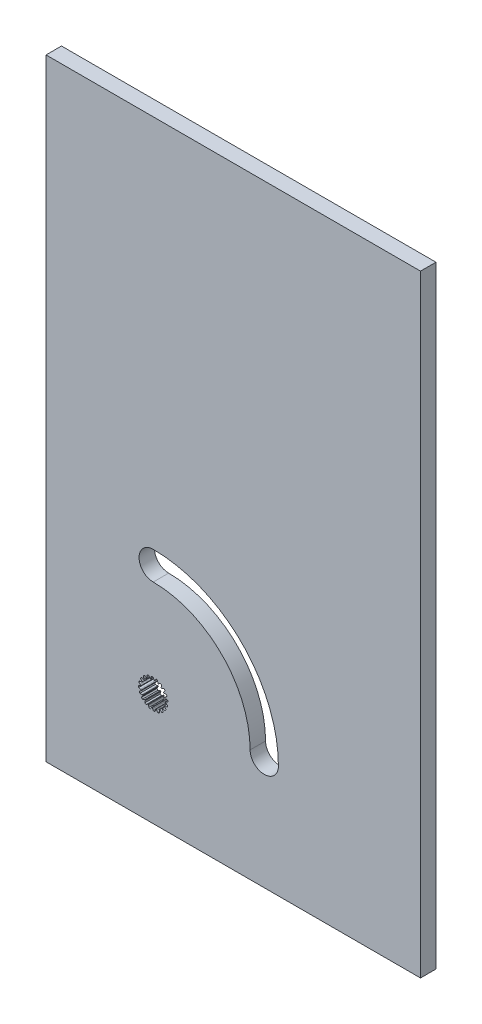
SolidWorks part; units mm, degrees
ref_plane "Ön Düzlem" through (0, 0, 0) normal (0, 0, 1) x (1, 0, 0)
ref_plane "Üst Düzlem" through (0, 0, 0) normal (0, 1, 0) x (1, 0, 0)
ref_plane "Sağ Düzlem" through (0, 0, 0) normal (1, 0, 0) x (0, 0, -1)
sketch "Çizim1" plane through (0, 0, 0) normal (0, 0, 1) x (1, 0, 0)
  line L1 (-41.8204, 26.3508) -> (30.9359, 26.3508)
  line L2 (-41.8204, 26.3508) -> (-41.8204, -92.5962)
  line L3 (-41.8204, -92.5962) -> (30.9359, -92.5962)
  line L4 (30.9359, 26.3508) -> (30.9359, -92.5962)
  point P11 (-21.6285, -56.4542)
extrude "Yükseklik-Ekstrüzyon1" add sketch "Çizim1" along normal blind 3
sketch "Çizim4" plane through (0, 0, 0) normal (0, 0, -1) x (-1, 0, 0)
  line L0 (20.655, -68.2535) -> (20.4495, -67.9708)
  line L1 (20.1545, -68.0456) -> (20.1085, -68.392)
  line L2 (20.1085, -68.392) -> (20.1196, -68.5886)
  line L3 (20.0301, -68.627) -> (19.8953, -68.4835)
  line L4 (19.8953, -68.4835) -> (19.6125, -68.2782)
  line L5 (19.355, -68.4404) -> (19.4183, -68.7841)
  line L6 (19.4183, -68.7841) -> (19.4896, -68.9677)
  line L7 (19.4164, -69.0318) -> (19.2438, -68.937)
  line L8 (19.2438, -68.937) -> (18.9114, -68.8291)
  line L9 (18.7167, -69.063) -> (18.8831, -69.3703)
  line L10 (18.8831, -69.3703) -> (19.0076, -69.5229)
  line L11 (18.9578, -69.6065) -> (18.7644, -69.5697)
  line L12 (18.7644, -69.5697) -> (18.4149, -69.5698)
  line L13 (18.302, -69.8524) -> (18.5552, -70.0933)
  line L14 (18.5552, -70.0933) -> (18.7207, -70.1998)
  line L15 (18.6992, -70.2948) -> (18.5039, -70.3195)
  line L16 (18.5039, -70.3195) -> (18.1716, -70.4276)
  line L17 (18.1515, -70.7313) -> (18.4668, -70.8821)
  line L18 (18.4668, -70.8821) -> (18.6571, -70.9323)
  line L19 (18.666, -71.0293) -> (18.4879, -71.1132)
  line L20 (18.4879, -71.1132) -> (18.2052, -71.3187)
  line L21 (18.28, -71.6137) -> (18.6264, -71.6597)
  line L22 (18.6264, -71.6597) -> (18.823, -71.6486)
  line L23 (18.8614, -71.7381) -> (18.7179, -71.8729)
  line L24 (18.7179, -71.8729) -> (18.5126, -72.1557)
  line L25 (18.6749, -72.4132) -> (19.0185, -72.3499)
  line L26 (19.0185, -72.3499) -> (19.2021, -72.2786)
  line L27 (19.2662, -72.3518) -> (19.1715, -72.5244)
  line L28 (19.1715, -72.5244) -> (19.0636, -72.8568)
  line L29 (19.2975, -73.0515) -> (19.6048, -72.8851)
  line L30 (19.6048, -72.8851) -> (19.7573, -72.7606)
  line L31 (19.8409, -72.8104) -> (19.8041, -73.0038)
  line L32 (19.8041, -73.0038) -> (19.8042, -73.3533)
  line L33 (20.0868, -73.4662) -> (20.3277, -73.213)
  line L34 (20.3277, -73.213) -> (20.4343, -73.0474)
  line L35 (20.5292, -73.069) -> (20.554, -73.2643)
  line L36 (20.554, -73.2643) -> (20.6621, -73.5966)
  line L37 (20.9657, -73.6167) -> (21.1165, -73.3014)
  line L38 (21.1165, -73.3014) -> (21.1668, -73.111)
  line L39 (21.2637, -73.1022) -> (21.3476, -73.2803)
  line L40 (21.3476, -73.2803) -> (21.5531, -73.563)
  line L41 (21.8481, -73.4882) -> (21.8941, -73.1418)
  line L42 (21.8941, -73.1418) -> (21.883, -72.9452)
  line L43 (21.9725, -72.9068) -> (22.1074, -73.0503)
  line L44 (22.1074, -73.0503) -> (22.3901, -73.2556)
  line L45 (22.6476, -73.0933) -> (22.5843, -72.7496)
  line L46 (22.5843, -72.7496) -> (22.513, -72.5661)
  line L47 (22.5862, -72.5019) -> (22.7588, -72.5967)
  line L48 (22.7588, -72.5967) -> (23.0912, -72.7046)
  line L49 (23.2859, -72.4707) -> (23.1195, -72.1634)
  line L50 (23.1195, -72.1634) -> (22.995, -72.0109)
  line L51 (23.0448, -71.9273) -> (23.2383, -71.9641)
  line L52 (23.2383, -71.9641) -> (23.5877, -71.964)
  line L53 (23.7006, -71.6813) -> (23.4474, -71.4405)
  line L54 (23.4474, -71.4405) -> (23.2819, -71.3339)
  line L55 (23.3034, -71.239) -> (23.4987, -71.2142)
  line L56 (23.4987, -71.2142) -> (23.831, -71.1061)
  line L57 (23.8511, -70.8025) -> (23.5359, -70.6516)
  line L58 (23.5359, -70.6516) -> (23.3455, -70.6014)
  line L59 (23.3366, -70.5045) -> (23.5147, -70.4206)
  line L60 (23.5147, -70.4206) -> (23.7974, -70.2151)
  line L61 (23.7226, -69.9201) -> (23.3762, -69.8741)
  line L62 (23.3762, -69.8741) -> (23.1796, -69.8851)
  line L63 (23.1412, -69.7957) -> (23.2847, -69.6608)
  line L64 (23.2847, -69.6608) -> (23.49, -69.3781)
  line L65 (23.3277, -69.1206) -> (22.9841, -69.1839)
  line L66 (22.9841, -69.1839) -> (22.8005, -69.2552)
  line L67 (22.7364, -69.1819) -> (22.8312, -69.0094)
  line L68 (22.8312, -69.0094) -> (22.939, -68.677)
  line L69 (22.7052, -68.4823) -> (22.3979, -68.6487)
  line L70 (22.3979, -68.6487) -> (22.2453, -68.7732)
  line L71 (22.1617, -68.7233) -> (22.1985, -68.5299)
  line L72 (22.1985, -68.5299) -> (22.1984, -68.1805)
  line L73 (21.9158, -68.0676) -> (21.6749, -68.3208)
  line L74 (21.6749, -68.3208) -> (21.5683, -68.4863)
  line L75 (21.4734, -68.4648) -> (21.4486, -68.2695)
  line L76 (21.4486, -68.2695) -> (21.3406, -67.9371)
  line L77 (21.0369, -67.9171) -> (20.8861, -68.2323)
  line L78 (20.8861, -68.2323) -> (20.8359, -68.4227)
  line L79 (20.7389, -68.4316) -> (20.655, -68.2535)
  line L80 (20.5686, -68.3046) -> (20.4067, -68.0819)
  line L81 (20.2451, -68.1229) -> (20.2089, -68.3958)
  line L82 (20.2089, -68.3958) -> (20.2235, -68.6556)
  line L83 (20.0071, -68.7485) -> (19.8289, -68.5589)
  line L84 (19.8289, -68.5589) -> (19.6061, -68.3971)
  line L85 (19.4651, -68.486) -> (19.5149, -68.7567)
  line L86 (19.5149, -68.7567) -> (19.6091, -68.9993)
  line L87 (19.432, -69.1545) -> (19.2039, -69.0292)
  line L88 (19.2039, -69.0292) -> (18.9421, -68.9442)
  line L89 (18.8354, -69.0723) -> (18.9665, -69.3144)
  line L90 (18.9665, -69.3144) -> (19.1311, -69.516)
  line L91 (19.0106, -69.7183) -> (18.7549, -69.6697)
  line L92 (18.7549, -69.6697) -> (18.4796, -69.6698)
  line L93 (18.4178, -69.8245) -> (18.6173, -70.0143)
  line L94 (18.6173, -70.0143) -> (18.8361, -70.1552)
  line L95 (18.784, -70.3848) -> (18.5258, -70.4176)
  line L96 (18.5258, -70.4176) -> (18.264, -70.5027)
  line L97 (18.253, -70.669) -> (18.5014, -70.7878)
  line L98 (18.5014, -70.7878) -> (18.753, -70.8542)
  line L99 (18.7744, -71.0887) -> (18.539, -71.1996)
  line L100 (18.539, -71.1996) -> (18.3164, -71.3615)
  line L101 (18.3573, -71.5231) -> (18.6302, -71.5593)
  line L102 (18.6302, -71.5593) -> (18.89, -71.5447)
  line L103 (18.9829, -71.7611) -> (18.7933, -71.9393)
  line L104 (18.7933, -71.9393) -> (18.6315, -72.1621)
  line L105 (18.7204, -72.3031) -> (18.9912, -72.2532)
  line L106 (18.9912, -72.2532) -> (19.2337, -72.159)
  line L107 (19.3889, -72.3362) -> (19.2637, -72.5643)
  line L108 (19.2637, -72.5643) -> (19.1787, -72.8261)
  line L109 (19.3067, -72.9327) -> (19.5488, -72.8017)
  line L110 (19.5488, -72.8017) -> (19.7504, -72.6371)
  line L111 (19.9528, -72.7576) -> (19.9041, -73.0133)
  line L112 (19.9041, -73.0133) -> (19.9042, -73.2886)
  line L113 (20.059, -73.3504) -> (20.2487, -73.1509)
  line L114 (20.2487, -73.1509) -> (20.3896, -72.9321)
  line L115 (20.6193, -72.9842) -> (20.652, -73.2424)
  line L116 (20.652, -73.2424) -> (20.7371, -73.5042)
  line L117 (20.9034, -73.5151) -> (21.0223, -73.2668)
  line L118 (21.0223, -73.2668) -> (21.0886, -73.0152)
  line L119 (21.3232, -72.9937) -> (21.434, -73.2291)
  line L120 (21.434, -73.2291) -> (21.5959, -73.4518)
  line L121 (21.7575, -73.4109) -> (21.7937, -73.138)
  line L122 (21.7937, -73.138) -> (21.7791, -72.8782)
  line L123 (21.9955, -72.7853) -> (22.1738, -72.9749)
  line L124 (22.1738, -72.9749) -> (22.3965, -73.1367)
  line L125 (22.5375, -73.0478) -> (22.4877, -72.777)
  line L126 (22.4877, -72.777) -> (22.3935, -72.5345)
  line L127 (22.5706, -72.3793) -> (22.7987, -72.5045)
  line L128 (22.7987, -72.5045) -> (23.0605, -72.5895)
  line L129 (23.1672, -72.4614) -> (23.0361, -72.2193)
  line L130 (23.0361, -72.2193) -> (22.8715, -72.0178)
  line L131 (22.9921, -71.8154) -> (23.2477, -71.8641)
  line L132 (23.2477, -71.8641) -> (23.523, -71.864)
  line L133 (23.5848, -71.7092) -> (23.3853, -71.5195)
  line L134 (23.3853, -71.5195) -> (23.1666, -71.3786)
  line L135 (23.2186, -71.1489) -> (23.4768, -71.1162)
  line L136 (23.4768, -71.1162) -> (23.7386, -71.0311)
  line L137 (23.7496, -70.8647) -> (23.5012, -70.7459)
  line L138 (23.5012, -70.7459) -> (23.2496, -70.6796)
  line L139 (23.2282, -70.445) -> (23.4636, -70.3341)
  line L140 (23.4636, -70.3341) -> (23.6863, -70.1723)
  line L141 (23.6453, -70.0107) -> (23.3724, -69.9744)
  line L142 (23.3724, -69.9744) -> (23.1126, -69.9891)
  line L143 (23.0197, -69.7726) -> (23.2093, -69.5944)
  line L144 (23.2093, -69.5944) -> (23.3711, -69.3717)
  line L145 (23.2822, -69.2307) -> (23.0115, -69.2805)
  line L146 (23.0115, -69.2805) -> (22.7689, -69.3747)
  line L147 (22.6137, -69.1976) -> (22.739, -68.9695)
  line L148 (22.739, -68.9695) -> (22.824, -68.7076)
  line L149 (22.6959, -68.601) -> (22.4538, -68.7321)
  line L150 (22.4538, -68.7321) -> (22.2522, -68.8966)
  line L151 (22.0498, -68.7761) -> (22.0985, -68.5205)
  line L152 (22.0985, -68.5205) -> (22.0984, -68.2452)
  line L153 (21.9436, -68.1834) -> (21.7539, -68.3828)
  line L154 (21.7539, -68.3828) -> (21.613, -68.6016)
  line L155 (21.3833, -68.5496) -> (21.3506, -68.2914)
  line L156 (21.3506, -68.2914) -> (21.2655, -68.0296)
  line L157 (21.0992, -68.0186) -> (20.9804, -68.267)
  line L158 (20.9804, -68.267) -> (20.914, -68.5186)
  line L159 (20.6795, -68.54) -> (20.5686, -68.3046)
  line L160 (20.5686, -68.3046) -> (20.4067, -68.0819)
  line L161 (20.2451, -68.1229) -> (20.2089, -68.3958)
  line L162 (20.2089, -68.3958) -> (20.2235, -68.6556)
  line L163 (20.0071, -68.7485) -> (19.8289, -68.5589)
  line L164 (19.8289, -68.5589) -> (19.6061, -68.3971)
  line L165 (19.4651, -68.486) -> (19.5149, -68.7567)
  line L166 (19.5149, -68.7567) -> (19.6091, -68.9993)
  line L167 (19.432, -69.1545) -> (19.2039, -69.0292)
  line L168 (19.2039, -69.0292) -> (18.9421, -68.9442)
  line L169 (18.8354, -69.0723) -> (18.9665, -69.3144)
  line L170 (18.9665, -69.3144) -> (19.1311, -69.516)
  line L171 (19.0106, -69.7183) -> (18.7549, -69.6697)
  line L172 (18.7549, -69.6697) -> (18.4796, -69.6698)
  line L173 (18.4178, -69.8245) -> (18.6173, -70.0143)
  line L174 (18.6173, -70.0143) -> (18.8361, -70.1552)
  line L175 (18.784, -70.3848) -> (18.5258, -70.4176)
  line L176 (18.5258, -70.4176) -> (18.264, -70.5027)
  line L177 (18.253, -70.669) -> (18.5014, -70.7878)
  line L178 (18.5014, -70.7878) -> (18.753, -70.8542)
  line L179 (18.7744, -71.0887) -> (18.539, -71.1996)
  line L180 (18.539, -71.1996) -> (18.3164, -71.3615)
  line L181 (18.3573, -71.5231) -> (18.6302, -71.5593)
  line L182 (18.6302, -71.5593) -> (18.89, -71.5447)
  line L183 (18.9829, -71.7611) -> (18.7933, -71.9393)
  line L184 (18.7933, -71.9393) -> (18.6315, -72.1621)
  line L185 (18.7204, -72.3031) -> (18.9912, -72.2532)
  line L186 (18.9912, -72.2532) -> (19.2337, -72.159)
  line L187 (19.3889, -72.3362) -> (19.2637, -72.5643)
  line L188 (19.2637, -72.5643) -> (19.1787, -72.8261)
  line L189 (19.3067, -72.9327) -> (19.5488, -72.8017)
  line L190 (19.5488, -72.8017) -> (19.7504, -72.6371)
  line L191 (19.9528, -72.7576) -> (19.9041, -73.0133)
  line L192 (19.9041, -73.0133) -> (19.9042, -73.2886)
  line L193 (20.059, -73.3504) -> (20.2487, -73.1509)
  line L194 (20.2487, -73.1509) -> (20.3896, -72.9321)
  line L195 (20.6193, -72.9842) -> (20.652, -73.2424)
  line L196 (20.652, -73.2424) -> (20.7371, -73.5042)
  line L197 (20.9034, -73.5151) -> (21.0223, -73.2668)
  line L198 (21.0223, -73.2668) -> (21.0886, -73.0152)
  line L199 (21.3232, -72.9937) -> (21.434, -73.2291)
  line L200 (21.434, -73.2291) -> (21.5959, -73.4518)
  line L201 (21.7575, -73.4109) -> (21.7937, -73.138)
  line L202 (21.7937, -73.138) -> (21.7791, -72.8782)
  line L203 (21.9955, -72.7853) -> (22.1738, -72.9749)
  line L204 (22.1738, -72.9749) -> (22.3965, -73.1367)
  line L205 (22.5375, -73.0478) -> (22.4877, -72.777)
  line L206 (22.4877, -72.777) -> (22.3935, -72.5345)
  line L207 (22.5706, -72.3793) -> (22.7987, -72.5045)
  line L208 (22.7987, -72.5045) -> (23.0605, -72.5895)
  line L209 (23.1672, -72.4614) -> (23.0361, -72.2193)
  line L210 (23.0361, -72.2193) -> (22.8715, -72.0178)
  line L211 (22.9921, -71.8154) -> (23.2477, -71.8641)
  line L212 (23.2477, -71.8641) -> (23.523, -71.864)
  line L213 (23.5848, -71.7092) -> (23.3853, -71.5195)
  line L214 (23.3853, -71.5195) -> (23.1666, -71.3786)
  line L215 (23.2186, -71.1489) -> (23.4768, -71.1162)
  line L216 (23.4768, -71.1162) -> (23.7386, -71.0311)
  line L217 (23.7496, -70.8647) -> (23.5012, -70.7459)
  line L218 (23.5012, -70.7459) -> (23.2496, -70.6796)
  line L219 (23.2282, -70.445) -> (23.4636, -70.3341)
  line L220 (23.4636, -70.3341) -> (23.6863, -70.1723)
  line L221 (23.6453, -70.0107) -> (23.3724, -69.9744)
  line L222 (23.3724, -69.9744) -> (23.1126, -69.9891)
  line L223 (23.0197, -69.7726) -> (23.2093, -69.5944)
  line L224 (23.2093, -69.5944) -> (23.3711, -69.3717)
  line L225 (23.2822, -69.2307) -> (23.0115, -69.2805)
  line L226 (23.0115, -69.2805) -> (22.7689, -69.3747)
  line L227 (22.6137, -69.1976) -> (22.739, -68.9695)
  line L228 (22.739, -68.9695) -> (22.824, -68.7076)
  line L229 (22.6959, -68.601) -> (22.4538, -68.7321)
  line L230 (22.4538, -68.7321) -> (22.2522, -68.8966)
  line L231 (22.0498, -68.7761) -> (22.0985, -68.5205)
  line L232 (22.0985, -68.5205) -> (22.0984, -68.2452)
  line L233 (21.9436, -68.1834) -> (21.7539, -68.3828)
  line L234 (21.7539, -68.3828) -> (21.613, -68.6016)
  line L235 (21.3833, -68.5496) -> (21.3506, -68.2914)
  line L236 (21.3506, -68.2914) -> (21.2655, -68.0296)
  line L237 (21.0992, -68.0186) -> (20.9804, -68.267)
  line L238 (20.9804, -68.267) -> (20.914, -68.5186)
  line L239 (20.6795, -68.54) -> (20.5686, -68.3046)
  arc A0 (20.4495, -67.9708) -> (20.1545, -68.0456) centre (21.0013, -70.7669) ccw
  arc A1 (20.1196, -68.5886) -> (20.0301, -68.627) centre (21.0013, -70.7669) ccw
  arc A2 (19.6125, -68.2782) -> (19.355, -68.4404) centre (21.0013, -70.7669) ccw
  arc A3 (19.4896, -68.9677) -> (19.4164, -69.0318) centre (21.0013, -70.7669) ccw
  arc A4 (18.9114, -68.8291) -> (18.7167, -69.063) centre (21.0013, -70.7669) ccw
  arc A5 (19.0076, -69.5229) -> (18.9578, -69.6065) centre (21.0013, -70.7669) ccw
  arc A6 (18.4149, -69.5698) -> (18.302, -69.8524) centre (21.0013, -70.7669) ccw
  arc A7 (18.7207, -70.1998) -> (18.6992, -70.2948) centre (21.0013, -70.7669) ccw
  arc A8 (18.1716, -70.4276) -> (18.1515, -70.7313) centre (21.0013, -70.7669) ccw
  arc A9 (18.6571, -70.9323) -> (18.666, -71.0293) centre (21.0013, -70.7669) ccw
  arc A10 (18.2052, -71.3187) -> (18.28, -71.6137) centre (21.0013, -70.7669) ccw
  arc A11 (18.823, -71.6486) -> (18.8614, -71.7381) centre (21.0013, -70.7669) ccw
  arc A12 (18.5126, -72.1557) -> (18.6749, -72.4132) centre (21.0013, -70.7669) ccw
  arc A13 (19.2021, -72.2786) -> (19.2662, -72.3518) centre (21.0013, -70.7669) ccw
  arc A14 (19.0636, -72.8568) -> (19.2975, -73.0515) centre (21.0013, -70.7669) ccw
  arc A15 (19.7573, -72.7606) -> (19.8409, -72.8104) centre (21.0013, -70.7669) ccw
  arc A16 (19.8042, -73.3533) -> (20.0868, -73.4662) centre (21.0013, -70.7669) ccw
  arc A17 (20.4343, -73.0474) -> (20.5292, -73.069) centre (21.0013, -70.7669) ccw
  arc A18 (20.6621, -73.5966) -> (20.9657, -73.6167) centre (21.0013, -70.7669) ccw
  arc A19 (21.1668, -73.111) -> (21.2637, -73.1022) centre (21.0013, -70.7669) ccw
  arc A20 (21.5531, -73.563) -> (21.8481, -73.4882) centre (21.0013, -70.7669) ccw
  arc A21 (21.883, -72.9452) -> (21.9725, -72.9068) centre (21.0013, -70.7669) ccw
  arc A22 (22.3901, -73.2556) -> (22.6476, -73.0933) centre (21.0013, -70.7669) ccw
  arc A23 (22.513, -72.5661) -> (22.5862, -72.5019) centre (21.0013, -70.7669) ccw
  arc A24 (23.0912, -72.7046) -> (23.2859, -72.4707) centre (21.0013, -70.7669) ccw
  arc A25 (22.995, -72.0109) -> (23.0448, -71.9273) centre (21.0013, -70.7669) ccw
  arc A26 (23.5877, -71.964) -> (23.7006, -71.6813) centre (21.0013, -70.7669) ccw
  arc A27 (23.2819, -71.3339) -> (23.3034, -71.239) centre (21.0013, -70.7669) ccw
  arc A28 (23.831, -71.1061) -> (23.8511, -70.8025) centre (21.0013, -70.7669) ccw
  arc A29 (23.3455, -70.6014) -> (23.3366, -70.5045) centre (21.0013, -70.7669) ccw
  arc A30 (23.7974, -70.2151) -> (23.7226, -69.9201) centre (21.0013, -70.7669) ccw
  arc A31 (23.1796, -69.8851) -> (23.1412, -69.7957) centre (21.0013, -70.7669) ccw
  arc A32 (23.49, -69.3781) -> (23.3277, -69.1206) centre (21.0013, -70.7669) ccw
  arc A33 (22.8005, -69.2552) -> (22.7364, -69.1819) centre (21.0013, -70.7669) ccw
  arc A34 (22.939, -68.677) -> (22.7052, -68.4823) centre (21.0013, -70.7669) ccw
  arc A35 (22.2453, -68.7732) -> (22.1617, -68.7233) centre (21.0013, -70.7669) ccw
  arc A36 (22.1984, -68.1805) -> (21.9158, -68.0676) centre (21.0013, -70.7669) ccw
  arc A37 (21.5683, -68.4863) -> (21.4734, -68.4648) centre (21.0013, -70.7669) ccw
  arc A38 (21.3406, -67.9371) -> (21.0369, -67.9171) centre (21.0013, -70.7669) ccw
  arc A39 (20.8359, -68.4227) -> (20.7389, -68.4316) centre (21.0013, -70.7669) ccw
  arc A40 (20.4067, -68.0819) -> (20.2451, -68.1229) centre (21.0013, -70.7669) ccw
  arc A41 (20.2235, -68.6556) -> (20.0071, -68.7485) centre (21.0013, -70.7669) ccw
  arc A42 (19.6061, -68.3971) -> (19.4651, -68.486) centre (21.0013, -70.7669) ccw
  arc A43 (19.6091, -68.9993) -> (19.432, -69.1545) centre (21.0013, -70.7669) ccw
  arc A44 (18.9421, -68.9442) -> (18.8354, -69.0723) centre (21.0013, -70.7669) ccw
  arc A45 (19.1311, -69.516) -> (19.0106, -69.7183) centre (21.0013, -70.7669) ccw
  arc A46 (18.4796, -69.6698) -> (18.4178, -69.8245) centre (21.0013, -70.7669) ccw
  arc A47 (18.8361, -70.1552) -> (18.784, -70.3848) centre (21.0013, -70.7669) ccw
  arc A48 (18.264, -70.5027) -> (18.253, -70.669) centre (21.0013, -70.7669) ccw
  arc A49 (18.753, -70.8542) -> (18.7744, -71.0887) centre (21.0013, -70.7669) ccw
  arc A50 (18.3164, -71.3615) -> (18.3573, -71.5231) centre (21.0013, -70.7669) ccw
  arc A51 (18.89, -71.5447) -> (18.9829, -71.7611) centre (21.0013, -70.7669) ccw
  arc A52 (18.6315, -72.1621) -> (18.7204, -72.3031) centre (21.0013, -70.7669) ccw
  arc A53 (19.2337, -72.159) -> (19.3889, -72.3362) centre (21.0013, -70.7669) ccw
  arc A54 (19.1787, -72.8261) -> (19.3067, -72.9327) centre (21.0013, -70.7669) ccw
  arc A55 (19.7504, -72.6371) -> (19.9528, -72.7576) centre (21.0013, -70.7669) ccw
  arc A56 (19.9042, -73.2886) -> (20.059, -73.3504) centre (21.0013, -70.7669) ccw
  arc A57 (20.3896, -72.9321) -> (20.6193, -72.9842) centre (21.0013, -70.7669) ccw
  arc A58 (20.7371, -73.5042) -> (20.9034, -73.5151) centre (21.0013, -70.7669) ccw
  arc A59 (21.0886, -73.0152) -> (21.3232, -72.9937) centre (21.0013, -70.7669) ccw
  arc A60 (21.5959, -73.4518) -> (21.7575, -73.4109) centre (21.0013, -70.7669) ccw
  arc A61 (21.7791, -72.8782) -> (21.9955, -72.7853) centre (21.0013, -70.7669) ccw
  arc A62 (22.3965, -73.1367) -> (22.5375, -73.0478) centre (21.0013, -70.7669) ccw
  arc A63 (22.3935, -72.5345) -> (22.5706, -72.3793) centre (21.0013, -70.7669) ccw
  arc A64 (23.0605, -72.5895) -> (23.1672, -72.4614) centre (21.0013, -70.7669) ccw
  arc A65 (22.8715, -72.0178) -> (22.9921, -71.8154) centre (21.0013, -70.7669) ccw
  arc A66 (23.523, -71.864) -> (23.5848, -71.7092) centre (21.0013, -70.7669) ccw
  arc A67 (23.1666, -71.3786) -> (23.2186, -71.1489) centre (21.0013, -70.7669) ccw
  arc A68 (23.7386, -71.0311) -> (23.7496, -70.8647) centre (21.0013, -70.7669) ccw
  arc A69 (23.2496, -70.6796) -> (23.2282, -70.445) centre (21.0013, -70.7669) ccw
  arc A70 (23.6863, -70.1723) -> (23.6453, -70.0107) centre (21.0013, -70.7669) ccw
  arc A71 (23.1126, -69.9891) -> (23.0197, -69.7726) centre (21.0013, -70.7669) ccw
  arc A72 (23.3711, -69.3717) -> (23.2822, -69.2307) centre (21.0013, -70.7669) ccw
  arc A73 (22.7689, -69.3747) -> (22.6137, -69.1976) centre (21.0013, -70.7669) ccw
  arc A74 (22.824, -68.7076) -> (22.6959, -68.601) centre (21.0013, -70.7669) ccw
  arc A75 (22.2522, -68.8966) -> (22.0498, -68.7761) centre (21.0013, -70.7669) ccw
  arc A76 (22.0984, -68.2452) -> (21.9436, -68.1834) centre (21.0013, -70.7669) ccw
  arc A77 (21.613, -68.6016) -> (21.3833, -68.5496) centre (21.0013, -70.7669) ccw
  arc A78 (21.2655, -68.0296) -> (21.0992, -68.0186) centre (21.0013, -70.7669) ccw
  arc A79 (20.914, -68.5186) -> (20.6795, -68.54) centre (21.0013, -70.7669) ccw
  arc A80 (20.4067, -68.0819) -> (20.2451, -68.1229) centre (21.0013, -70.7669) ccw
  arc A81 (20.2235, -68.6556) -> (20.0071, -68.7485) centre (21.0013, -70.7669) ccw
  arc A82 (19.6061, -68.3971) -> (19.4651, -68.486) centre (21.0013, -70.7669) ccw
  arc A83 (19.6091, -68.9993) -> (19.432, -69.1545) centre (21.0013, -70.7669) ccw
  arc A84 (18.9421, -68.9442) -> (18.8354, -69.0723) centre (21.0013, -70.7669) ccw
  arc A85 (19.1311, -69.516) -> (19.0106, -69.7183) centre (21.0013, -70.7669) ccw
  arc A86 (18.4796, -69.6698) -> (18.4178, -69.8245) centre (21.0013, -70.7669) ccw
  arc A87 (18.8361, -70.1552) -> (18.784, -70.3848) centre (21.0013, -70.7669) ccw
  arc A88 (18.264, -70.5027) -> (18.253, -70.669) centre (21.0013, -70.7669) ccw
  arc A89 (18.753, -70.8542) -> (18.7744, -71.0887) centre (21.0013, -70.7669) ccw
  arc A90 (18.3164, -71.3615) -> (18.3573, -71.5231) centre (21.0013, -70.7669) ccw
  arc A91 (18.89, -71.5447) -> (18.9829, -71.7611) centre (21.0013, -70.7669) ccw
  arc A92 (18.6315, -72.1621) -> (18.7204, -72.3031) centre (21.0013, -70.7669) ccw
  arc A93 (19.2337, -72.159) -> (19.3889, -72.3362) centre (21.0013, -70.7669) ccw
  arc A94 (19.1787, -72.8261) -> (19.3067, -72.9327) centre (21.0013, -70.7669) ccw
  arc A95 (19.7504, -72.6371) -> (19.9528, -72.7576) centre (21.0013, -70.7669) ccw
  arc A96 (19.9042, -73.2886) -> (20.059, -73.3504) centre (21.0013, -70.7669) ccw
  arc A97 (20.3896, -72.9321) -> (20.6193, -72.9842) centre (21.0013, -70.7669) ccw
  arc A98 (20.7371, -73.5042) -> (20.9034, -73.5151) centre (21.0013, -70.7669) ccw
  arc A99 (21.0886, -73.0152) -> (21.3232, -72.9937) centre (21.0013, -70.7669) ccw
  arc A100 (21.5959, -73.4518) -> (21.7575, -73.4109) centre (21.0013, -70.7669) ccw
  arc A101 (21.7791, -72.8782) -> (21.9955, -72.7853) centre (21.0013, -70.7669) ccw
  arc A102 (22.3965, -73.1367) -> (22.5375, -73.0478) centre (21.0013, -70.7669) ccw
  arc A103 (22.3935, -72.5345) -> (22.5706, -72.3793) centre (21.0013, -70.7669) ccw
  arc A104 (23.0605, -72.5895) -> (23.1672, -72.4614) centre (21.0013, -70.7669) ccw
  arc A105 (22.8715, -72.0178) -> (22.9921, -71.8154) centre (21.0013, -70.7669) ccw
  arc A106 (23.523, -71.864) -> (23.5848, -71.7092) centre (21.0013, -70.7669) ccw
  arc A107 (23.1666, -71.3786) -> (23.2186, -71.1489) centre (21.0013, -70.7669) ccw
  arc A108 (23.7386, -71.0311) -> (23.7496, -70.8647) centre (21.0013, -70.7669) ccw
  arc A109 (23.2496, -70.6796) -> (23.2282, -70.445) centre (21.0013, -70.7669) ccw
  arc A110 (23.6863, -70.1723) -> (23.6453, -70.0107) centre (21.0013, -70.7669) ccw
  arc A111 (23.1126, -69.9891) -> (23.0197, -69.7726) centre (21.0013, -70.7669) ccw
  arc A112 (23.3711, -69.3717) -> (23.2822, -69.2307) centre (21.0013, -70.7669) ccw
  arc A113 (22.7689, -69.3747) -> (22.6137, -69.1976) centre (21.0013, -70.7669) ccw
  arc A114 (22.824, -68.7076) -> (22.6959, -68.601) centre (21.0013, -70.7669) ccw
  arc A115 (22.2522, -68.8966) -> (22.0498, -68.7761) centre (21.0013, -70.7669) ccw
  arc A116 (22.0984, -68.2452) -> (21.9436, -68.1834) centre (21.0013, -70.7669) ccw
  arc A117 (21.613, -68.6016) -> (21.3833, -68.5496) centre (21.0013, -70.7669) ccw
  arc A118 (21.2655, -68.0296) -> (21.0992, -68.0186) centre (21.0013, -70.7669) ccw
  arc A119 (20.914, -68.5186) -> (20.6795, -68.54) centre (21.0013, -70.7669) ccw
  arc A440 (20.4067, -68.0819) -> (20.2451, -68.1229) centre (21.0013, -70.7669) ccw construction
  dimension "D1" = 0
  dimension "D2" = 0.1
extrude "Kes-Ekstrüzyon3" cut sketch "Çizim4" against normal through all contours L238 A119 L239 L160 A80 L161 L162 A81 L163 L164 A82 L165 L166 A83 L167 L168 A84 L169 L170 A85 L171 L172 A86 L173 L174 A87 L175 L176 A88 L177 L178 A89 L179 L180 A90 L181 L182 A91 L183 L184 A92 L185 L186 A93 L187 L188 A94 L189 L190 A95 L191 | L78 A39 L79 L0 A0 L1 L2 A1 L3 L4 A2 L5 L6 A3 L7 L8 A4 L9 L10 A5 L11 L12 A6 L13 L14 A7 L15 L16 A8 L17 L18 A9 L19 L20 A10 L21 L22 A11 L23 L24 A12 L25 L26 A13 L27 L28 A14 L29 L30 A15 L31
sketch "Sketch1" plane through (0, 0, 3) normal (0, 0, 1) x (1, 0, 0)
  arc A0 (-21.0013, -49.1869) -> (0.5787, -70.7669) centre (-21.0013, -70.7669) cw construction
  arc A1 (3.3287, -70.7669) -> (-21.0013, -46.4369) centre (-21.0013, -70.7669) ccw
  arc A2 (-2.1713, -70.7669) -> (-21.0013, -51.9369) centre (-21.0013, -70.7669) ccw
  arc A3 (-2.1713, -70.7669) -> (3.3287, -70.7669) centre (0.5787, -70.7669) ccw
  arc A4 (-21.0013, -46.4369) -> (-21.0013, -51.9369) centre (-21.0013, -49.1869) ccw
  circle A5 centre (-21.0013, -70.7669) radius 2.85 construction
  arc A6 (-21.8481, -73.4882) -> (-21.5531, -73.563) centre (-21.0013, -70.7669) ccw construction
  point P3 (-5.7419, -55.5075)
  point P10 (-21.0105, -70.8472)
  point P14 (-21.0013, -70.7669)
  point P15 (0, 0)
  point P16 (0, 0)
  dimension "D1" = 21.58
  dimension "D2" = 2.75
extrude "Cut-Extrude1" cut sketch "Sketch1" against normal through all
